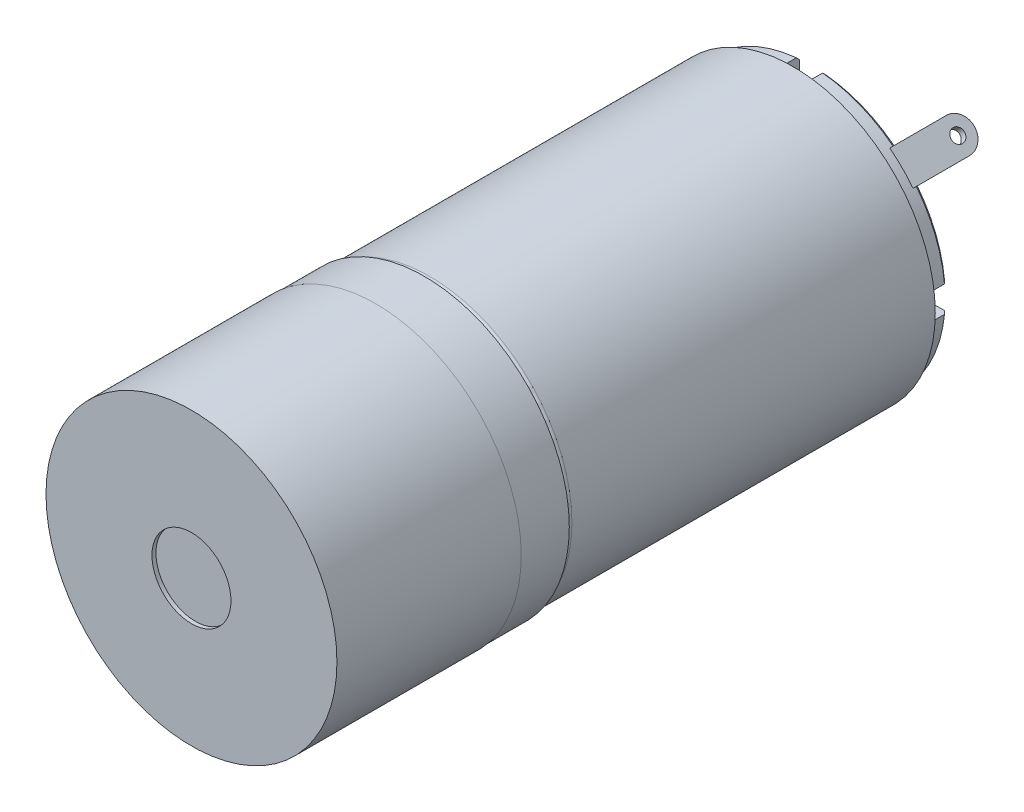
SolidWorks part; units mm, degrees
ref_plane "Front Plane" through (0, 0, 0) normal (0, 0, 1) x (1, 0, 0)
ref_plane "Top Plane" through (0, 0, 0) normal (0, 1, 0) x (1, 0, 0)
ref_plane "Right Plane" through (0, 0, 0) normal (1, 0, 0) x (0, 0, -1)
sketch "Sketch1" plane through (0, 0, 0) normal (0, 0, 1) x (1, 0, 0)
  circle A0 centre (0, 0) radius 11
  dimension "D1" = 22
extrude "Boss-Extrude1" add sketch "Sketch1" along normal mid plane 40.9
ref_plane "Plane1" through (0, 0, 9.05) normal (0, 0, -1) x (-1, 0, 0)
sketch "Sketch2" plane through (0, 0, 9.05) normal (0, 0, -1) x (-1, 0, 0)
  circle A0 centre (0, 0) radius 10.8
  circle A1 centre (0, 0) radius 11
  dimension "D1" = 22
  dimension "D2" = 21.6
extrude "Cut-Extrude1" cut sketch "Sketch2" along normal through all
ref_axis "Axis2" through (0, 0, -27.7585) along (0, 0, 1)
sketch "Sketch3" plane through (0, 0, 0) normal (1, 0, 0) x (0, 0, -1)
  line L0 (-9.05, 10.4) -> (-9.05, 10.3)
  line L1 (-8.55, 10.8) -> (-9.05, 10.8)
  line L2 (-9.05, -10.8) -> (-9.05, 10.8) construction
  line L3 (-9.05, 10.3) -> (-8.55, 10.3) construction
  line L4 (-8.55, 10.3) -> (-8.55, 10.8) construction
  line L5 (-8.55, 10.8) -> (-8.65, 10.8)
  line L6 (-9.05, -11) -> (-9.05, 11) construction
  line L7 (-9.05, 10.8) -> (-9.05, 10.3)
  arc A0 (-9.05, 10.4) -> (-8.65, 10.8) centre (-8.65, 10.4) cw
  dimension "D3" = 0.4
  dimension "D1" = 10.3
  dimension "D2" = 0.5
sketch "Sketch5" plane through (0, 0, 20.45) normal (0, 0, 1) x (1, 0, 0)
  line L0 (-1.5, 9) -> (-1.5, 10.8972)
  line L1 (1.5, 9) -> (1.5, 10.8972)
  line L2 (9, 1.5) -> (10.8972, 1.5)
  line L3 (9, -1.5) -> (10.8972, -1.5)
  line L4 (1.5, -9) -> (1.5, -10.8972)
  line L5 (-1.5, -9) -> (-1.5, -10.8972)
  line L6 (-9, -1.5) -> (-10.8972, -1.5)
  line L7 (-9, 1.5) -> (-10.8972, 1.5)
  circle A0 centre (0, 0) radius 9 construction
  arc A2 (-1.5, 9) -> (1.5, 9) centre (0, 9) ccw
  arc A3 (1.5, 10.8972) -> (-1.5, 10.8972) centre (0, 0) ccw
  arc A4 (9, 1.5) -> (9, -1.5) centre (9, 0) ccw
  arc A5 (10.8972, -1.5) -> (10.8972, 1.5) centre (0, 0) ccw
  arc A6 (1.5, -9) -> (-1.5, -9) centre (0, -9) ccw
  arc A7 (-1.5, -10.8972) -> (1.5, -10.8972) centre (0, 0) ccw
  arc A8 (-9, -1.5) -> (-9, 1.5) centre (-9, 0) ccw
  arc A9 (-10.8972, 1.5) -> (-10.8972, -1.5) centre (0, 0) ccw
  circle A10 centre (-6.364, 6.364) radius 0.8
  circle A11 centre (6.364, 6.364) radius 0.8
  circle A12 centre (6.364, -6.364) radius 0.8
  circle A13 centre (-6.364, -6.364) radius 0.8
  point P26 (0, 0)
  point P35 (0, 0)
  dimension "D1" = 18
  dimension "D2" = 1.5
  dimension "D3" = 11
  dimension "D6" = 1.6
  dimension "D5" = 45
  dimension "D4" = 4
  dimension "D7" = 4
extrude "Cut-Extrude2" cut sketch "Sketch5" against normal blind 3
revolve "Cut-Revolve3" cut sketch "Sketch3" angle 360 about axis through (0, 0, -27.7585) along (0, 0, 1)
sketch "Sketch6" plane through (0, 0, 20.45) normal (0, 0, 1) x (1, 0, 0)
  line L0 (-6, -3.6056) -> (-6, 3.6056)
  line L1 (6, -3.6056) -> (6, 3.6056)
  arc A0 (-6, -3.6056) -> (6, -3.6056) centre (0, 0) ccw
  arc A1 (6, 3.6056) -> (-6, 3.6056) centre (0, 0) ccw
  point P6 (-6, 0)
  point P9 (6, 0)
  dimension "D1" = 14
  dimension "D2" = 6
  dimension "D3" = 6
extrude "Boss-Extrude2" add sketch "Sketch6" along normal blind 2
sketch "Sketch7" plane through (0, 0, 22.45) normal (0, 0, 1) x (1, 0, 0)
  circle A0 centre (0, 0) radius 3
  dimension "D1" = 6
extrude "Boss-Extrude3" add sketch "Sketch7" along normal blind 12
ref_plane "Plane3" through (0, 0, 17.45) normal (0, 0, 1) x (1, 0, 0)
ref_plane "Plane4" through (0, 9, 0) normal (0, 1, 0) x (1, 0, 0)
sketch "Sketch9" plane through (0, 9, 0) normal (0, 1, 0) x (1, 0, 0)
  line L0 (0, -17.45) -> (0, -18.65)
  line L1 (-15.9774, -17.45) -> (15.9774, -17.45) construction
  line L2 (0, 27.7585) -> (0, -44.3925) construction
  line L3 (0, -18.65) -> (0.85, -18.65)
  line L4 (1.3, -18.2) -> (1.3, -17.45)
  line L5 (1.3, -17.45) -> (0, -17.45)
  arc A0 (1.3, -18.2) -> (0.85, -18.65) centre (0.85, -18.2) cw
  dimension "D1" = 0.45
  dimension "D2" = 1.3
  dimension "D3" = 1.2
revolve "Revolve1" add sketch "Sketch9" angle 360 about L0
sketch "Sketch10" plane through (0, 0, 18.65) normal (0, 0, 1) x (1, 0, 0)
  line L0 (0.15, 9.15) -> (1.2913, 9.15)
  line L2 (0, 7) -> (0, 11) construction
  line L4 (-1.2913, 8.85) -> (-0.15, 8.85)
  line L6 (-1.2913, 9.15) -> (-0.15, 9.15)
  line L8 (0.15, 8.85) -> (1.2913, 8.85)
  line L9 (2, 9) -> (-2, 9) construction
  line L10 (-0.15, 9.15) -> (0.15, 9.15)
  line L11 (0.15, 8.85) -> (-0.15, 8.85)
  arc A0 (-1.2913, 9.15) -> (-1.2913, 8.85) centre (0, 9) ccw
  arc A2 (1.2913, 8.85) -> (1.2913, 9.15) centre (0, 9) ccw
  point P18 (0, 9)
  point P21 (0, 9)
  dimension "D3" = 4
  dimension "D4" = 4
  dimension "D7" = 0.15
  dimension "D8" = 0.15
extrude "Cut-Extrude3" cut sketch "Sketch10" against normal blind 1
pattern_circular "CirPattern1" count 4 every 90 about axis through (0, 0, 0) along (0, 0, 1) of "Revolve1"
pattern_circular "CirPattern2" count 4 every 90 about axis through (0, 0, -27.7585) along (0, 0, 1) of "Cut-Extrude3"
sketch "Sketch11" plane through (0, 0, 22.45) normal (0, 0, 1) x (1, 0, 0)
  circle A0 centre (0, 0) radius 5
  dimension "D1" = 10
extrude "Boss-Extrude4" add sketch "Sketch11" along normal blind 0.25
ref_plane "Plane5" through (0, 0, 19.75) normal (0, 0, -1) x (-1, 0, 0)
sketch "Sketch12" plane through (0, 0, 19.75) normal (0, 0, -1) x (-1, 0, 0)
  circle A0 centre (0, 0) radius 11.05
extrude "Boss-Extrude5" add sketch "Sketch12" along normal mid plane 14
sketch "Sketch14" plane through (0, 0, 0) normal (1, 0, 0) x (0, 0, -1)
  line L0 (27.7585, 0) -> (-44.3925, 0) construction
  line L1 (-34.45, 3) -> (-34.45, -3) construction
  circle A0 centre (-30.35, 0) radius 1.0375
  dimension "D1" = 2.075
  dimension "D2" = 4.1
extrude "Cut-Extrude4" cut sketch "Sketch14" against normal mid plane 6
sketch "Sketch16" plane through (0, 0, -20.45) normal (0, 0, -1) x (-1, 0, 0)
  circle A0 centre (0, 0) radius 10.8
  circle A1 centre (0, 0) radius 10.3
  dimension "D1" = 21.6
  dimension "D2" = 20.6
extrude "Cut-Extrude5" cut sketch "Sketch16" against normal blind 1.5
sketch "Sketch17" plane through (0, 0, -20.45) normal (0, 0, -1) x (-1, 0, 0)
  line L0 (0, 8) -> (-1, 8)
  line L1 (-1, 8) -> (-1, 10.2513)
  line L2 (0, 0) -> (0, 12.1687) construction
  line L3 (0, 8) -> (1, 8)
  line L4 (1, 8) -> (1, 10.2513)
  line L5 (8, 1) -> (10.2513, 1)
  line L6 (8, 0) -> (8, 1)
  line L7 (8, 0) -> (8, -1)
  line L8 (8, -1) -> (10.2513, -1)
  line L9 (1, -8) -> (1, -10.2513)
  line L10 (0, -8) -> (1, -8)
  line L11 (0, -8) -> (-1, -8)
  line L12 (-1, -8) -> (-1, -10.2513)
  line L13 (-8, -1) -> (-10.2513, -1)
  line L14 (-8, 0) -> (-8, -1)
  line L15 (-8, 0) -> (-8, 1)
  line L16 (-8, 1) -> (-10.2513, 1)
  arc A0 (1, 10.2513) -> (-1, 10.2513) centre (0, 0) ccw
  arc A1 (10.2513, -1) -> (10.2513, 1) centre (0, 0) ccw
  arc A2 (-1, -10.2513) -> (1, -10.2513) centre (0, 0) ccw
  arc A3 (-10.2513, 1) -> (-10.2513, -1) centre (0, 0) ccw
  point P25 (0, 0)
  dimension "D1" = 10.3
  dimension "D2" = 8
  dimension "D3" = 1
  dimension "D4" = 1
  dimension "D5" = 4
extrude "Cut-Extrude6" cut sketch "Sketch17" against normal blind 0.5
sketch "Sketch18" plane through (0, 0, -20.45) normal (0, 0, -1) x (-1, 0, 0)
  line L0 (-1, 10.2513) -> (-1, 9.4472)
  line L2 (1, 10.2513) -> (1, 9.4472)
  line L4 (10.2513, 1) -> (9.4472, 1)
  line L5 (10.2513, -1) -> (9.4472, -1)
  line L6 (1, -10.2513) -> (1, -9.4472)
  line L7 (-1, -10.2513) -> (-1, -9.4472)
  line L8 (-10.2513, -1) -> (-9.4472, -1)
  line L9 (-10.2513, 1) -> (-9.4472, 1)
  arc A0 (1, 9.4472) -> (-1, 9.4472) centre (0, 0) ccw
  arc A1 (1, 10.2513) -> (-1, 10.2513) centre (0, 0) ccw
  arc A2 (9.4472, -1) -> (9.4472, 1) centre (0, 0) ccw
  arc A3 (10.2513, -1) -> (10.2513, 1) centre (0, 0) ccw
  arc A4 (-1, -9.4472) -> (1, -9.4472) centre (0, 0) ccw
  arc A5 (-1, -10.2513) -> (1, -10.2513) centre (0, 0) ccw
  arc A6 (-9.4472, 1) -> (-9.4472, -1) centre (0, 0) ccw
  arc A7 (-10.2513, 1) -> (-10.2513, -1) centre (0, 0) ccw
  point P23 (0, 0)
  dimension "D1" = 4
extrude "Cut-Extrude7" cut sketch "Sketch18" against normal blind 1.5
chamfer "Chamfer1" distance 0.25 angle 45 2 edges at (-7.2832, 7.2832, -20.45) (7.2832, -7.2832, -20.45)
sketch "Sketch19" plane through (0, 0, -20.45) normal (0, 0, -1) x (-1, 0, 0)
  line L0 (0, 0) -> (-7.4816, 7.4816) construction
  line L1 (-6.5453, 4.7776) -> (-8.3131, 6.5453)
  line L2 (-1, 8) -> (1, 8) construction
  line L3 (0, 0) -> (0, 8) construction
  line L4 (4.7776, -6.5453) -> (6.5453, -8.3131)
  line L5 (6.5453, -4.7776) -> (8.3131, -6.5453)
  line L6 (6.5453, -4.7776) -> (4.7776, -6.5453)
  line L14 (-4.7776, 6.5453) -> (-6.5453, 8.3131)
  line L15 (-6.5453, 4.7776) -> (-4.7776, 6.5453)
  arc A0 (6.5453, -8.3131) -> (8.3131, -6.5453) centre (0, 0) ccw
  arc A6 (-6.5453, 8.3131) -> (-8.3131, 6.5453) centre (0, 0) ccw
  point P1 (-7.6368, 7.6368)
  point P6 (-0.8839, -0.8839)
  point P7 (-8.5206, 6.7529)
  point P8 (0.8839, 0.8839)
  point P9 (-6.7529, 8.5206)
  point P13 (-5.6615, 5.6615)
  point P22 (0, 0)
  dimension "D1" = 45
  dimension "D3" = 8.0065
  dimension "D4" = 2.5
  dimension "D2" = 2
extrude "Cut-Extrude8" cut sketch "Sketch19" against normal blind 0.5
sketch "Sketch20" plane through (5.6615, 5.6615, 0) normal (0.7071, 0.7071, 0) x (0, 0, -1)
  line L0 (19.95, 1.25) -> (25.45, 1.25)
  line L1 (19.95, -1.25) -> (25.45, -1.25)
  line L2 (27.7585, 0) -> (-44.3925, 0) construction
  line L3 (19.95, -1.25) -> (19.95, 1.25) construction
  line L4 (19.95, -1.25) -> (19.95, 1.25)
  arc A0 (25.45, -1.25) -> (25.45, 1.25) centre (25.45, 0) ccw
  circle A1 centre (25.45, 0) radius 0.5
  dimension "D2" = 5.5
extrude "Boss-Extrude7" add sketch "Sketch20" along normal blind 0.5
pattern_circular "CirPattern4" count 2 every 180 about axis through (0, 0, 0) along (0, 0, 1) of "Boss-Extrude7"
sketch "Sketch22" plane through (0, 0, -20.45) normal (0, 0, -1) x (-1, 0, 0)
  circle A0 centre (0, 0) radius 3
  dimension "D1" = 6
extrude "Boss-Extrude8" add sketch "Sketch22" along normal blind 2
sketch "Sketch23" plane through (0, 0, -22.45) normal (0, 0, -1) x (-1, 0, 0)
  circle A0 centre (0, 0) radius 1
  dimension "D1" = 2
extrude "Boss-Extrude9" add sketch "Sketch23" along normal blind 9.2
chamfer "Chamfer2" distance 0.25 angle 45 1 edges at (-3, 0, -22.45)
sketch "Sketch24" plane through (0, 0, -31.65) normal (0, 0, -1) x (-1, 0, 0)
  circle A0 centre (0, 0) radius 1.5525
extrude "Cut-Extrude9" cut sketch "Sketch24" against normal blind 10
sketch "Sketch25" plane through (0, 0, 34.45) normal (0, 0, 1) x (1, 0, 0)
  circle A0 centre (0, 0) radius 3
extrude "Cut-Extrude10" cut sketch "Sketch25" against normal blind 8
